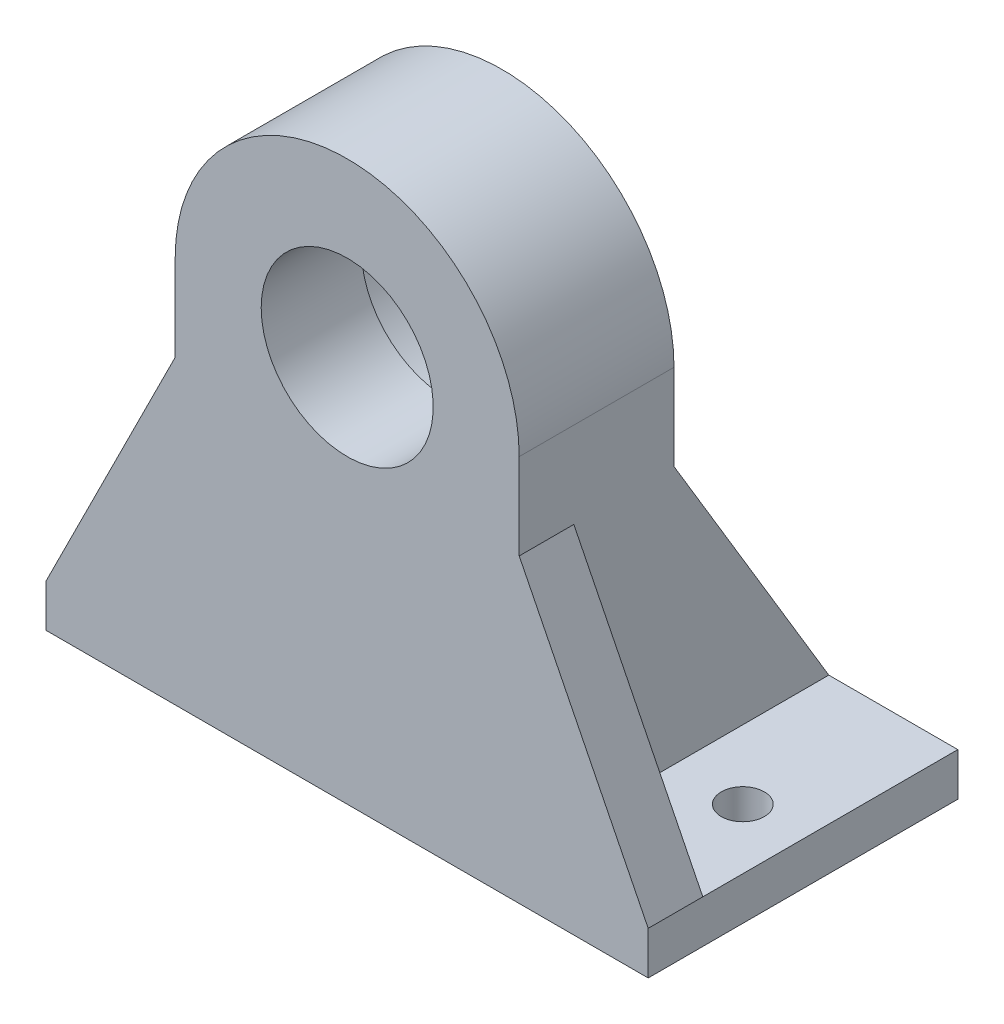
SolidWorks part; units mm, degrees
ref_plane "Front Plane" through (0, 0, 0) normal (0, 0, 1) x (1, 0, 0)
ref_plane "Top Plane" through (0, 0, 0) normal (0, 1, 0) x (1, 0, 0)
ref_plane "Right Plane" through (0, 0, 0) normal (1, 0, 0) x (0, 0, -1)
sketch "Sketch3" plane through (0, 0, 0) normal (0, 0, 1) x (1, 0, 0)
  line L0 (-20, 0) -> (-20, -40)
  line L1 (-20, -40) -> (20, -40)
  line L2 (20, -40) -> (20, 0)
  arc A0 (20, 0) -> (-20, 0) centre (0, 0) ccw
  dimension "D1" = 40
  dimension "D2" = 20
extrude "Boss-Extrude1" add sketch "Sketch3" along normal blind 18
sketch "Sketch6" plane through (0, -40, 0) normal (0, -1, 0) x (1, 0, 0)
  line L1 (-35, -18) -> (35, -18)
  line L2 (-35, -18) -> (-35, 18)
  line L3 (-35, 18) -> (35, 18)
  line L4 (35, -18) -> (35, 18)
  line L5 (-35, -18) -> (35, 18) construction
  line L6 (-35, 18) -> (35, -18) construction
  line L7 (-20, 18) -> (20, 18) construction
  line L10 (-28, 0) -> (-35, 0) construction
  line L11 (28, 0) -> (35, 0) construction
  line L12 (-20, 0) -> (20, 0) construction
  circle A0 centre (28, 0) radius 2.5
  circle A1 centre (-28, 0) radius 2.5
  point P6 (0, 0)
  dimension "D2" = 5
  dimension "D1" = 70
  dimension "D3" = 7
extrude "Boss-Extrude2" add sketch "Sketch6" along normal blind 5
sketch "Sketch7" plane through (0, 0, 0) normal (0, 0, -1) x (-1, 0, 0)
  circle A0 centre (0, 0) radius 10
  dimension "D1" = 20
extrude "Cut-Extrude1" cut sketch "Sketch7" against normal through all
sketch "Sketch8" plane through (0, 0, 0) normal (0, 0, -1) x (-1, 0, 0)
  circle A0 centre (0, 0) radius 14.2875
  dimension "D1" = 28.575
extrude "Cut-Extrude2" cut sketch "Sketch8" against normal blind 6.35
chamfer "Chamfer1" distance 0.5 angle 45 1 edges at (-14.2875, 0, 0)
sketch "Sketch9" plane through (20, 0, 0) normal (1, 0, 0) x (0, 0, -1)
  line L0 (18, -40) -> (0, -10)
  line L1 (0, -40) -> (0, 0) construction
  line L2 (0, -10) -> (0, -40)
  line L3 (0, -40) -> (18, -40)
  dimension "D1" = 30
extrude "Boss-Extrude3" add sketch "Sketch9" against normal blind 6.35
mirror "Mirror1" about plane through (0, 0, 0) normal (1, 0, 0) of "Boss-Extrude3"
sketch "Sketch10" plane through (0, 0, 18) normal (0, 0, 1) x (1, 0, 0)
  line L0 (-20, -10) -> (-35, -40)
  line L1 (-20, 0) -> (-20, -40) construction
  line L2 (-35, -40) -> (-20, -40)
  line L3 (-20, -40) -> (-20, -10)
  line L4 (20, -10) -> (20, -40)
  line L5 (20, -40) -> (20, 0) construction
  line L6 (20, -40) -> (35, -40)
  line L7 (35, -40) -> (20, -10)
  dimension "D1" = 30
extrude "Boss-Extrude4" add sketch "Sketch10" against normal blind 6.35
